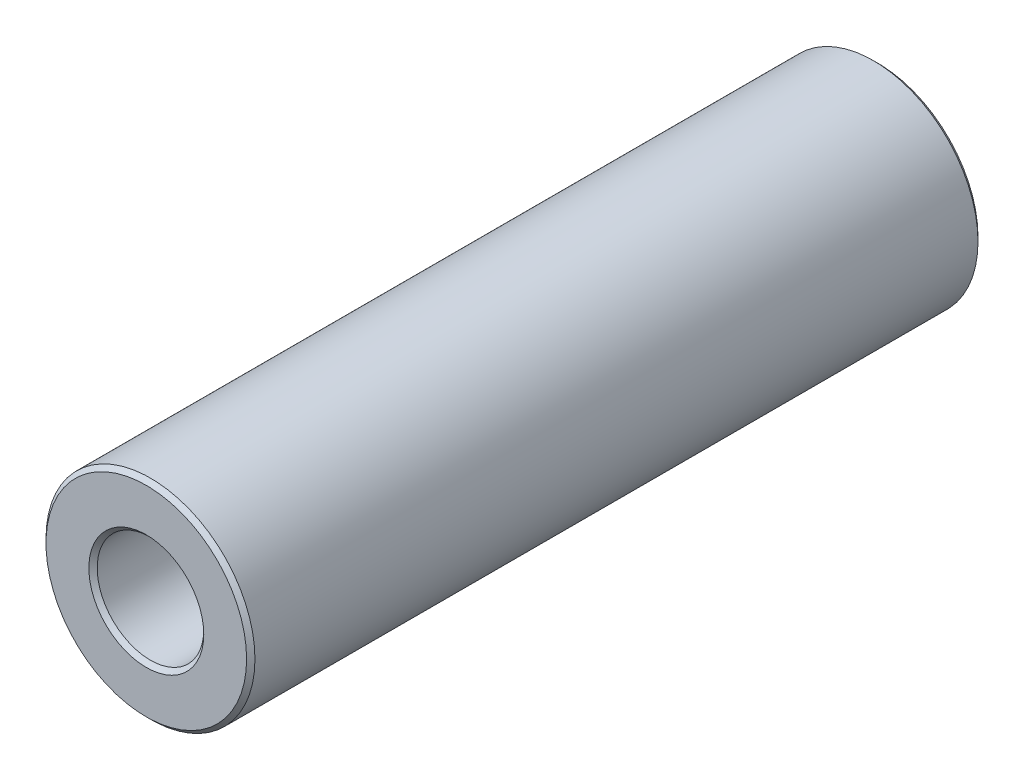
SolidWorks part; units mm, degrees
material "6061-T6 (SS)"
ref_plane "Front Plane" through (0, 0, 0) normal (0, 0, 1) x (1, 0, 0)
ref_plane "Top Plane" through (0, 0, 0) normal (0, 1, 0) x (1, 0, 0)
ref_plane "Right Plane" through (0, 0, 0) normal (1, 0, 0) x (0, 0, -1)
sketch "Sketch1" plane through (0, 0, 0) normal (0, 0, 1) x (1, 0, 0)
  circle A0 centre (0, 0) radius 2.55
  circle A1 centre (0, 0) radius 5
  dimension "D1" = 5.1
  dimension "D2" = 10
extrude "Boss-Extrude1" add sketch "Sketch1" along normal blind 35
chamfer "Chamfer1" distance 0.2 angle 45 4 edges at (5, 0, 0) (2.55, 0, 0) (2.55, 0, 35) (5, 0, 35)
